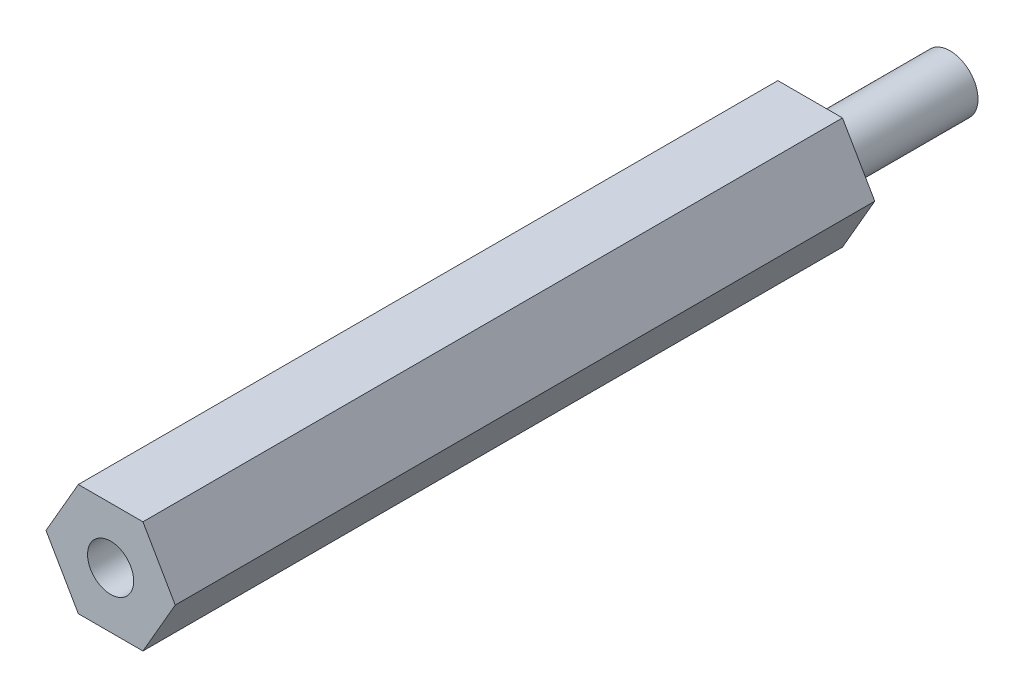
SolidWorks part; units mm, degrees
material "黃銅"
ref_plane "前基準面" through (0, 0, 0) normal (0, 0, 1) x (1, 0, 0)
ref_plane "上基準面" through (0, 0, 0) normal (0, 1, 0) x (1, 0, 0)
ref_plane "右基準面" through (0, 0, 0) normal (1, 0, 0) x (0, 0, -1)
sketch "草圖1" plane through (0, 0, 0) normal (0, 0, 1) x (1, 0, 0)
  line L1 (-2.3094, 4) -> (-4.6188, 0)
  line L2 (-4.6188, 0) -> (-2.3094, -4)
  line L3 (-2.3094, -4) -> (2.3094, -4)
  line L4 (2.3094, -4) -> (4.6188, 0)
  line L5 (4.6188, 0) -> (2.3094, 4)
  line L6 (2.3094, 4) -> (-2.3094, 4)
  circle A0 centre (0, 0) radius 4 construction
  dimension "D1" = 8
extrude "填料-伸長1" add sketch "草圖1" along normal blind 50
sketch "草圖4" plane through (0, 0, 0) normal (0, 0, -1) x (-1, 0, 0)
  circle A0 centre (0, 0) radius 2
  dimension "D1" = 4
extrude "填料-伸長2" add sketch "草圖4" along normal blind 10
hole_wizard "M4x0.7 螺紋孔1" positions "草圖2" profile "草圖3" tap size "M4x0.7" standard "Ansi Metric"
sketch "草圖2" plane through (0, 0, 50) normal (0, 0, 1) x (1, 0, 0)
  point P0 (0, 0)
sketch "草圖3" plane through (0, 0, 50) normal (1, 0, 0) x (0, -1, 0)
  line L0 (0, 0) -> (0, 11.0914)
  line L1 (0, 11.0914) -> (1.65, 10.1)
  line L2 (1.65, 10.1) -> (1.65, 0)
  line L5 (1.65, 0) -> (0, 0)
  line L10 (0, 11.0914) -> (-1.65, 10.1) construction
  line L11 (0, -6.35) -> (0, 107.95) construction
  dimension "螺孔鑽直徑" = 3.3
  dimension "螺孔鑽深度" = 10.1
  dimension "導頭角度" = 118
